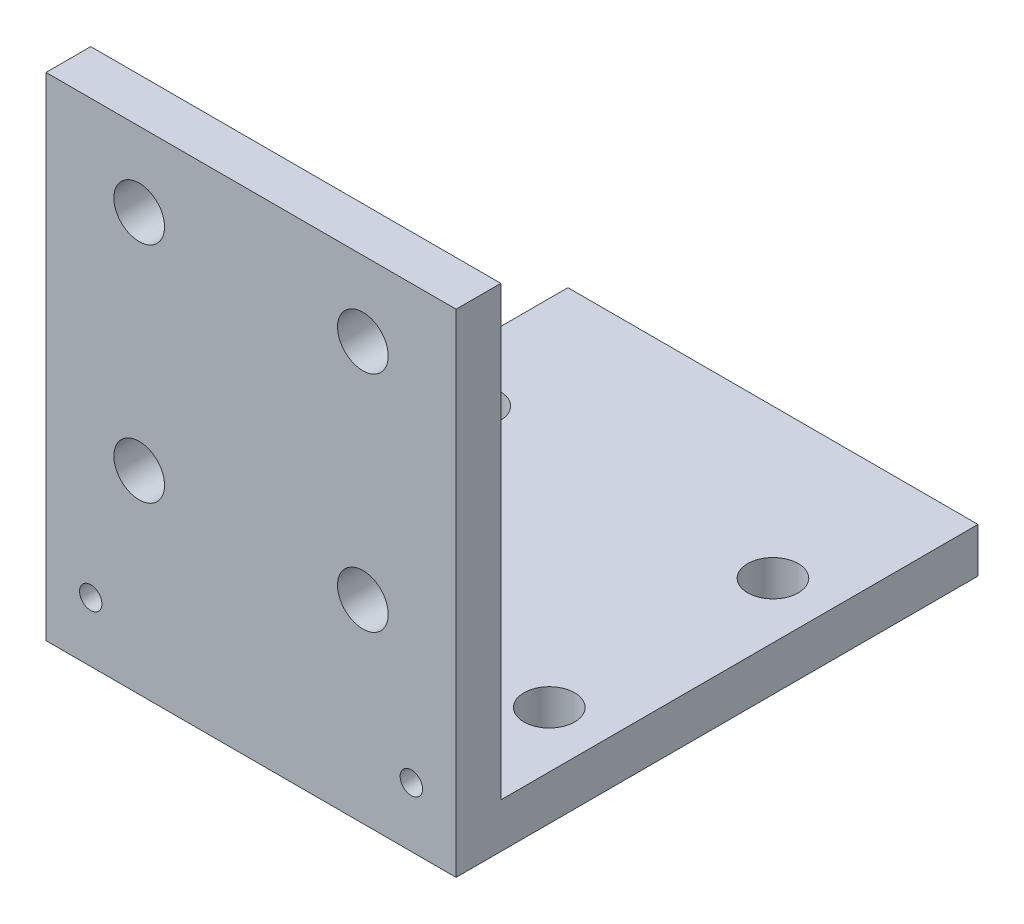
SolidWorks part; units mm, degrees
ref_plane "Front Plane" through (0, 0, 0) normal (0, 0, 1) x (1, 0, 0)
ref_plane "Top Plane" through (0, 0, 0) normal (0, 1, 0) x (1, 0, 0)
ref_plane "Right Plane" through (0, 0, 0) normal (1, 0, 0) x (0, 0, -1)
sketch "Sketch1" plane through (0, 0, 0) normal (0, 0, 1) x (1, 0, 0)
  line L1 (-13.75, 1.5) -> (13.75, 1.5)
  line L2 (-13.75, 1.5) -> (-13.75, -1.5)
  line L3 (-13.75, -1.5) -> (13.75, -1.5)
  line L4 (13.75, 1.5) -> (13.75, -1.5)
  line L5 (-13.75, 1.5) -> (13.75, -1.5) construction
  line L6 (-13.75, -1.5) -> (13.75, 1.5) construction
  point P0 (0, 0)
  dimension "D1" = 27.5
  dimension "D2" = 3
extrude "Boss-Extrude1" add sketch "Sketch1" along normal blind 35
sketch "Sketch2" plane through (0, 1.5, 0) normal (0, 1, 0) x (1, 0, 0)
  line L0 (-13.75, -32) -> (13.75, -32)
  line L1 (-13.75, -35) -> (-13.75, 0) construction
  line L2 (13.75, -35) -> (13.75, 0) construction
  line L3 (13.75, -35) -> (-13.75, -35) construction
  line L4 (13.75, -35) -> (-13.75, -35)
  line L5 (13.75, -35) -> (13.75, 0)
  line L6 (-13.75, -35) -> (-13.75, 0)
  line M3 (-13.75, 0) -> (-13.75, -35)
  line M4 (-13.75, -35) -> (13.75, -35)
  line M5 (13.75, -35) -> (13.75, 0)
  dimension "D1" = 3
extrude "Boss-Extrude2" add sketch "Sketch2" along normal blind 40 contours L0 M3 M4 M5
sketch "Sketch3" plane through (0, 1.5, 0) normal (0, 1, 0) x (1, 0, 0)
  line L0 (13.75, -35) -> (13.75, 0) construction
  line L1 (13.75, -35) -> (13.75, 0)
  line L6 (-13.75, 0) -> (-13.75, -32)
  line L7 (-13.75, -32) -> (13.75, -32)
  line L8 (13.75, -32) -> (13.75, 0)
  line L9 (13.75, 0) -> (-13.75, 0)
  line L10 (-13.75, 0) -> (-13.75, -32)
  line L11 (-13.75, -32) -> (13.75, -32)
  line L12 (13.75, -32) -> (13.75, 0)
  line L13 (13.75, 0) -> (-13.75, 0)
  circle A0 centre (10, -25) radius 1.7
  circle A1 centre (10, -10) radius 1.7
  circle A2 centre (-10, -10) radius 1.7
  circle A3 centre (-10, -25) radius 1.7
  point P8 (0, -17.5)
  point P11 (0, -17.5)
  dimension "D1" = 0
hole_wizard "M3 Clearance Hole1" positions "Sketch4" profile "Sketch5" hole size "M3" standard "ISO"
sketch "Sketch4" plane through (0, 1.5, 0) normal (0, 1, 0) x (1, 0, 0)
  point P0 (-10, -10)
  point P3 (-10, -25)
  point P6 (10, -25)
  point P9 (10, -10)
sketch "Sketch5" plane through (-10, 1.5, 10) normal (1, 0, 0) x (0, 0, 1)
  line L0 (0, 0) -> (0, 6.0215)
  line L1 (0, 6.0215) -> (1.7, 5)
  line L2 (1.7, 5) -> (1.7, 0)
  line L5 (1.7, 0) -> (0, 0)
  line L10 (0, 6.0215) -> (-1.7, 5) construction
  line L11 (0, -6.35) -> (0, 107.95) construction
  dimension "Hole Dia." = 3.4
  dimension "Hole Depth" = 5
  dimension "Drill Angle" = 118
sketch "Sketch6" plane through (0, 0, 35) normal (0, 0, 1) x (1, 0, 0)
  line L0 (-13.75, 41.5) -> (-13.75, -1.5) construction
  line L1 (-13.75, -1.5) -> (13.75, -1.5) construction
  circle A0 centre (-10.75, 2.5) radius 0.75
  dimension "D1" = 1.5
  dimension "D2" = 3
  dimension "D3" = 4
extrude "Cut-Extrude1" cut sketch "Sketch6" against normal blind 10
hole_wizard "M3 Clearance Hole2" positions "Sketch9" profile "Sketch10" hole size "M3" standard "ISO"
sketch "Sketch9" plane through (0, 0, 32) normal (0, 0, -1) x (-1, 0, 0)
  line L0 (13.75, 1.5) -> (-13.75, 1.5) construction
  point P0 (-7.5, 11.5)
  point P2 (7.5, 11.5)
  point P4 (7.5, 26.5)
  point P6 (-7.5, 26.5)
  point P17 (0, 1.5)
  dimension "D1" = 15
  dimension "D2" = 15
  dimension "D3" = 7.5
  dimension "D4" = 7.5
  dimension "D5" = 7.5
  dimension "D6" = 7.5
  dimension "D7" = 10
  dimension "D8" = 10
sketch "Sketch10" plane through (7.5, 11.5, 32) normal (1, 0, 0) x (0, 1, 0)
  line L0 (0, 0) -> (0, 6.0215)
  line L1 (0, 6.0215) -> (1.7, 5)
  line L2 (1.7, 5) -> (1.7, 0)
  line L5 (1.7, 0) -> (0, 0)
  line L10 (0, 6.0215) -> (-1.7, 5) construction
  line L11 (0, -6.35) -> (0, 107.95) construction
  dimension "Hole Dia." = 3.4
  dimension "Hole Depth" = 5
  dimension "Drill Angle" = 118
sketch "Sketch11" plane through (0, 0, 35) normal (0, 0, 1) x (1, 0, 0)
  line L4 (13.75, -1.5) -> (13.75, 41.5)
  line L5 (13.75, 41.5) -> (-13.75, 41.5)
  line L6 (-13.75, 41.5) -> (-13.75, -1.5)
  line L7 (-13.75, -1.5) -> (13.75, -1.5)
  line L8 (13.75, -1.5) -> (13.75, 41.5)
  line L9 (13.75, 41.5) -> (-13.75, 41.5)
  line L10 (-13.75, 41.5) -> (-13.75, -1.5)
  line L11 (-13.75, -1.5) -> (13.75, -1.5)
  circle A0 centre (7.5, 11.5) radius 1.7 construction
  circle A1 centre (7.5, 26.5) radius 1.7 construction
  circle A2 centre (-7.5, 26.5) radius 1.7 construction
  circle A3 centre (-7.5, 11.5) radius 1.7 construction
  circle A4 centre (7.5, 11.5) radius 1.7
  circle A5 centre (7.5, 26.5) radius 1.7
  circle A6 centre (-7.5, 26.5) radius 1.7
  circle A7 centre (-7.5, 11.5) radius 1.7
  dimension "D1" = 0
mirror "Mirror1" about plane through (0, 0, 0) normal (1, 0, 0) of "Cut-Extrude1"
sketch "Sketch12" plane through (0, 0, 32) normal (0, 0, -1) x (-1, 0, 0)
  line L0 (-13.75, 31.5) -> (13.75, 31.5)
  line L1 (-13.75, 41.5) -> (-13.75, 1.5) construction
  line L2 (13.75, 41.5) -> (13.75, 1.5) construction
  line L3 (13.75, 1.5) -> (-13.75, 1.5) construction
  line L8 (-13.75, 1.5) -> (13.75, 1.5)
  line L9 (13.75, 1.5) -> (13.75, 41.5)
  line L10 (13.75, 41.5) -> (-13.75, 41.5)
  line L11 (-13.75, 41.5) -> (-13.75, 1.5)
  line L12 (-13.75, 1.5) -> (13.75, 1.5)
  line L13 (13.75, 1.5) -> (13.75, 41.5)
  line L14 (13.75, 41.5) -> (-13.75, 41.5)
  line L15 (-13.75, 41.5) -> (-13.75, 1.5)
  line M9 (13.75, 1.5) -> (13.75, 41.5)
  line M10 (13.75, 41.5) -> (-13.75, 41.5)
  line M11 (-13.75, 41.5) -> (-13.75, 1.5)
  dimension "D1" = 30
  dimension "D2" = 0
extrude "Cut-Extrude2" cut sketch "Sketch12" against normal through all contours L0 M11 M9 M10
